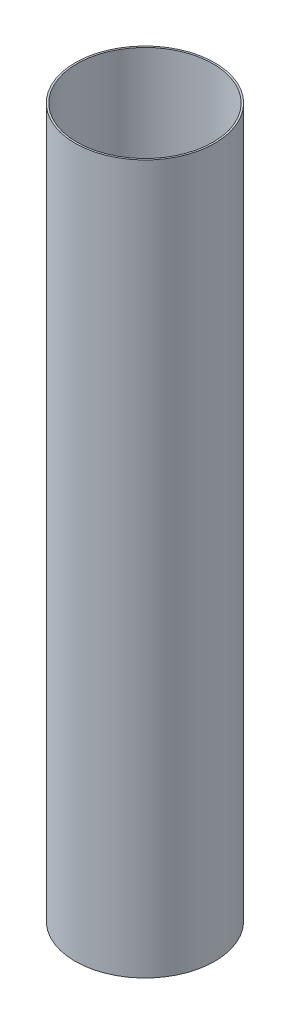
SolidWorks part; units mm, degrees
ref_plane "Front Plane" through (0, 0, 0) normal (0, 0, 1) x (1, 0, 0)
ref_plane "Top Plane" through (0, 0, 0) normal (0, 1, 0) x (1, 0, 0)
ref_plane "Right Plane" through (0, 0, 0) normal (1, 0, 0) x (0, 0, -1)
sketch "Sketch1" plane through (0, 0, 0) normal (0, 1, 0) x (1, 0, 0)
  circle A0 centre (0, 0) radius 20
  circle A1 centre (0, 0) radius 19.5
  dimension "D1" = 40
  dimension "D2" = 39
  dimension "D3" = 0.5
extrude "Boss-Extrude1" add sketch "Sketch1" along normal blind 203
